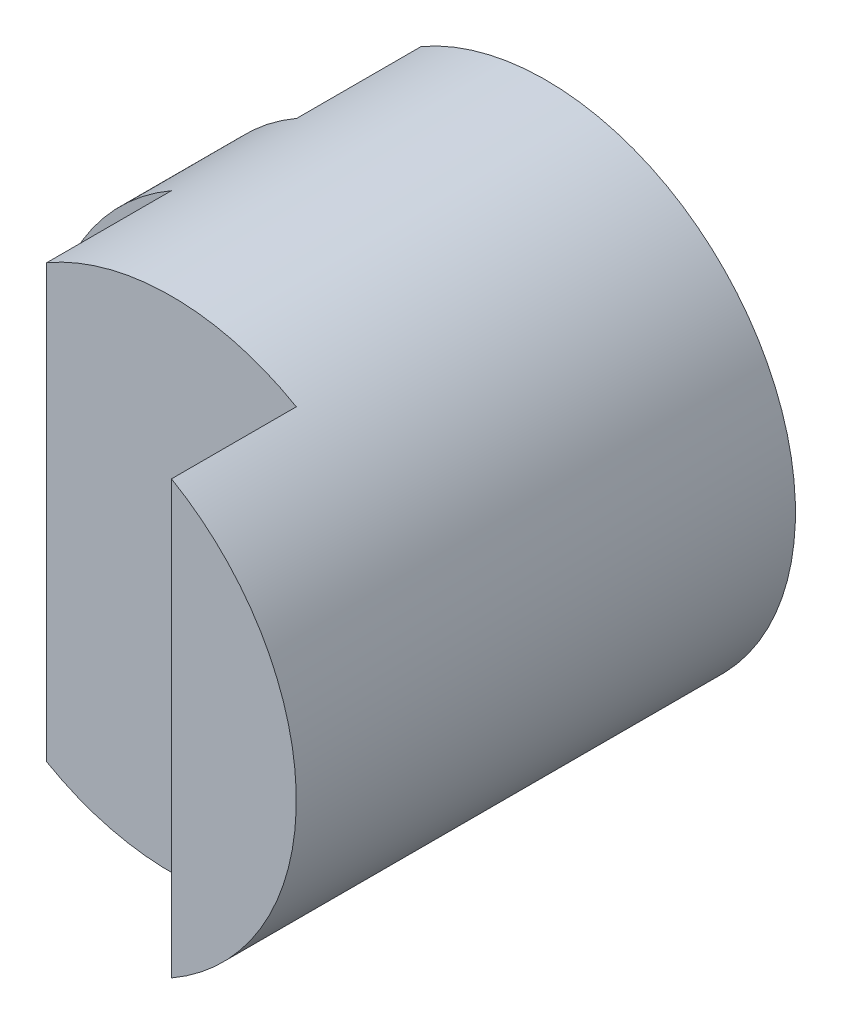
SolidWorks part; units mm, degrees
ref_plane "Front" through (0, 0, 0) normal (0, 0, 1) x (1, 0, 0)
ref_plane "Top" through (0, 0, 0) normal (0, 1, 0) x (1, 0, 0)
ref_plane "Right" through (0, 0, 0) normal (1, 0, 0) x (0, 0, -1)
sketch "Sketch1" plane through (0, 0, 0) normal (0, 0, 1) x (1, 0, 0)
  circle A0 centre (0, 0) radius 2
  dimension "D1" = 4
extrude "Boss-Extrude1" add sketch "Sketch1" along normal blind 4
sketch "Sketch2" plane through (0, 0, 0) normal (0, 1, 0) x (1, 0, 0)
  line L0 (-2, -4) -> (2, -4) construction
  line L1 (-1, -5) -> (1, -5)
  line L3 (-1, -3) -> (1, -3)
  line L4 (1, -5) -> (1, -3)
  line L5 (-1, -5) -> (1, -3) construction
  line L6 (-1, -3) -> (1, -5) construction
  line L8 (-1, -0.9964) -> (-2, -0.9964)
  line L9 (-2, 0) -> (-2, -4) construction
  line L11 (-2, -5) -> (-1, -5)
  line L12 (-2, -3) -> (-2, -5)
  line L13 (-2, -2) -> (-1, -2)
  line L17 (-1, -0.9964) -> (-1, 0)
  line L18 (-1, 0) -> (-2, 0)
  line L19 (-2, 0) -> (-2, -0.9964)
  line L20 (-1, -3) -> (-1, -2)
  line L21 (-2, -2) -> (-2, -3)
  point P0 (0, -4)
  dimension "D1" = 2
  dimension "D2" = 2
extrude "Cut-Extrude2" cut sketch "Sketch2" against normal mid plane 4
